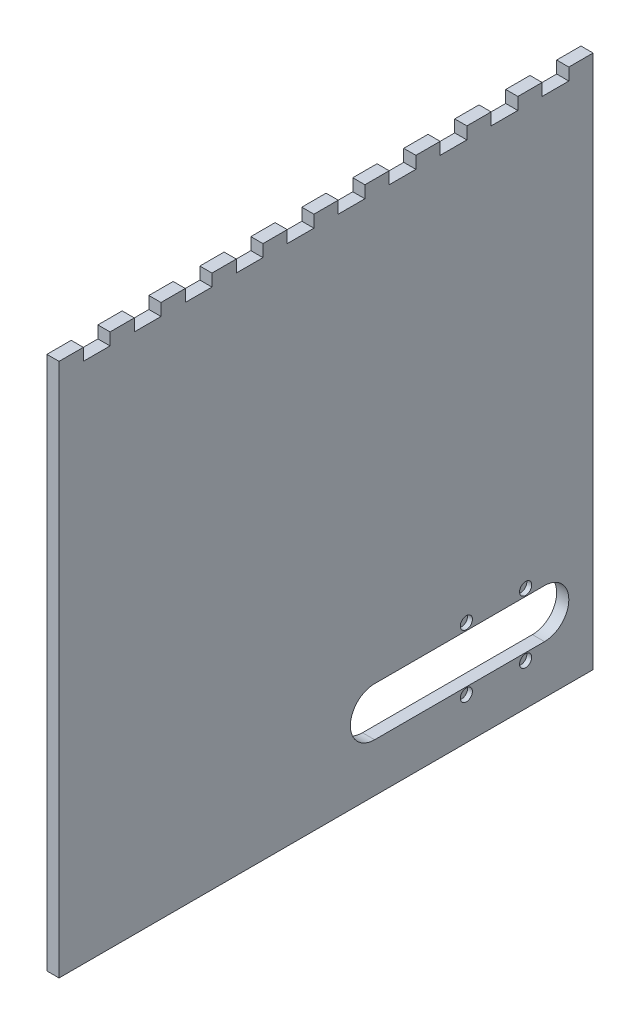
SolidWorks part; units mm, degrees
material "Acrylic (Medium-high impact)"
ref_plane "Front" through (0, 0, 0) normal (0, 0, 1) x (1, 0, 0)
ref_plane "Top" through (0, 0, 0) normal (0, 1, 0) x (1, 0, 0)
ref_plane "Right" through (0, 0, 0) normal (1, 0, 0) x (0, 0, -1)
sketch "Sketch1" plane through (0, 0, 0) normal (1, 0, 0) x (0, 0, -1)
  line L1 (-139.7, 142.875) -> (139.7, 142.875)
  line L2 (-139.7, 142.875) -> (-139.7, -142.875)
  line L3 (-139.7, -142.875) -> (139.7, -142.875)
  line L4 (139.7, 142.875) -> (139.7, -142.875)
  point P4 (-139.7, 0)
  point P6 (0, 142.875)
  dimension "D1" = 285.75
  dimension "D2" = 279.4
extrude "Boss-Extrude1" add sketch "Sketch1" along normal blind 6.35
sketch "Sketch2" plane through (6.35, 0, 0) normal (1, 0, 0) x (0, 0, -1)
  line L0 (139.7, -142.875) -> (139.7, 142.875) construction
  line L1 (-139.7, 142.875) -> (139.7, 142.875)
  line L2 (-139.7, 142.875) -> (-139.7, 136.525)
  line L3 (-139.7, 136.525) -> (139.7, 136.525)
  line L4 (139.7, 142.875) -> (139.7, 136.525)
  dimension "D1" = 6.35
extrude "Boss-Extrude2" add sketch "Sketch2" along normal blind 12.7
sketch "Sketch3" plane through (0, 0, 0) normal (-1, 0, 0) x (0, 0, 1)
  line L0 (-114.3, -85.725) -> (-25.4, -85.725)
  line L1 (-25.4, -111.125) -> (-114.3, -111.125)
  line L2 (12.7, 142.875) -> (12.7, -142.875) construction
  line L3 (-139.7, 142.875) -> (139.7, 142.875) construction
  line L4 (139.7, -142.875) -> (-139.7, -142.875) construction
  line L5 (139.7, 142.875) -> (139.7, -142.875) construction
  arc A0 (-25.4, -85.725) -> (-25.4, -111.125) centre (-25.4, -98.425) cw
  arc A1 (-114.3, -111.125) -> (-114.3, -85.725) centre (-114.3, -98.425) cw
  dimension "D1" = 25.4
  dimension "D3" = 88.9
  dimension "D2" = 38.1
  dimension "D4" = 127
  dimension "D5" = 44.45
extrude "Cut-Extrude1" cut sketch "Sketch3" against normal through all
sketch "Sketch4" plane through (0, 0, 0) normal (-1, 0, 0) x (0, 0, 1)
  line L0 (-113.03, 142.875) -> (-100.33, 142.875)
  line L1 (-139.7, 142.875) -> (-127, 142.875)
  line L2 (-139.7, 142.875) -> (-139.7, 136.525)
  line L3 (-139.7, 136.525) -> (-127, 136.525)
  line L4 (-127, 142.875) -> (-127, 136.525)
  line L5 (-113.03, 142.875) -> (-113.03, 136.525)
  line L6 (-113.03, 136.525) -> (-100.33, 136.525)
  line L7 (-100.33, 142.875) -> (-100.33, 136.525)
  line L8 (-86.36, 142.875) -> (-73.66, 142.875)
  line L9 (-86.36, 142.875) -> (-86.36, 136.525)
  line L10 (-86.36, 136.525) -> (-73.66, 136.525)
  line L11 (-73.66, 142.875) -> (-73.66, 136.525)
  line L12 (-59.69, 142.875) -> (-46.99, 142.875)
  line L13 (-59.69, 142.875) -> (-59.69, 136.525)
  line L14 (-59.69, 136.525) -> (-46.99, 136.525)
  line L15 (-46.99, 142.875) -> (-46.99, 136.525)
  line L16 (-33.02, 142.875) -> (-20.32, 142.875)
  line L17 (-33.02, 142.875) -> (-33.02, 136.525)
  line L18 (-33.02, 136.525) -> (-20.32, 136.525)
  line L19 (-20.32, 142.875) -> (-20.32, 136.525)
  line L20 (-6.35, 142.875) -> (6.35, 142.875)
  line L21 (-6.35, 142.875) -> (-6.35, 136.525)
  line L22 (-6.35, 136.525) -> (6.35, 136.525)
  line L23 (6.35, 142.875) -> (6.35, 136.525)
  line L24 (20.32, 142.875) -> (33.02, 142.875)
  line L25 (20.32, 142.875) -> (20.32, 136.525)
  line L26 (20.32, 136.525) -> (33.02, 136.525)
  line L27 (33.02, 142.875) -> (33.02, 136.525)
  line L28 (46.99, 142.875) -> (59.69, 142.875)
  line L29 (46.99, 142.875) -> (46.99, 136.525)
  line L30 (46.99, 136.525) -> (59.69, 136.525)
  line L31 (59.69, 142.875) -> (59.69, 136.525)
  line L32 (73.66, 142.875) -> (86.36, 142.875)
  line L33 (73.66, 142.875) -> (73.66, 136.525)
  line L34 (73.66, 136.525) -> (86.36, 136.525)
  line L35 (86.36, 142.875) -> (86.36, 136.525)
  line L36 (100.33, 142.875) -> (113.03, 142.875)
  line L37 (100.33, 142.875) -> (100.33, 136.525)
  line L38 (100.33, 136.525) -> (113.03, 136.525)
  line L39 (113.03, 142.875) -> (113.03, 136.525)
  line L40 (127, 142.875) -> (139.7, 142.875)
  line L41 (127, 142.875) -> (127, 136.525)
  line L42 (127, 136.525) -> (139.7, 136.525)
  line L43 (139.7, 142.875) -> (139.7, 136.525)
  line L69 (-139.7, 142.875) -> (139.7, 142.875)
  line L70 (-139.7, 142.875) -> (-139.7, 136.525)
  line L71 (-139.7, 136.525) -> (139.7, 136.525)
  line L72 (139.7, 142.875) -> (139.7, 136.525)
  line M74 (139.7, 142.875) -> (-139.7, 142.875)
  dimension "D1" = 6.35
  dimension "D2" = 12.7
  dimension "D3" = 11
sketch "Sketch5" plane through (0, 0, -139.7) normal (0, 0, -1) x (-1, 0, 0)
  line L1 (-6.35, 136.525) -> (-57.7651, 136.525)
  line L2 (-6.35, 136.525) -> (-6.35, 157.6842)
  line L3 (-6.35, 157.6842) -> (-57.7651, 157.6842)
  line L4 (-57.7651, 136.525) -> (-57.7651, 157.6842)
extrude "Cut-Extrude2" cut sketch "Sketch5" against normal through all
extrude "Cut-Extrude3" cut sketch "Sketch4" against normal blind 6.35 contours L4 L71 L5 M74 | L7 L71 L9 M74 | L11 L71 L13 M74 | L15 L71 L17 M74 | L19 L71 L21 M74 | L23 L71 L25 M74 | L27 L71 L29 M74 | L31 L71 L33 M74 | L35 L71 L37 M74 | L39 L71 L41 M74 | L69
sketch "Sketch6" plane through (6.35, 0, 0) normal (1, 0, 0) x (0, 0, -1)
  line L0 (77.9, -100.965) -> (77.9, -95.885)
  line L1 (99.9, -95.885) -> (99.9, -100.965)
  line L2 (71.9, -116.465) -> (71.9, -111.385)
  line L3 (74.9, -116.465) -> (74.9, -111.385)
  line L4 (71.9, -85.465) -> (71.9, -80.385)
  line L5 (74.9, -85.465) -> (74.9, -80.385)
  line L6 (88.9, -95.885) -> (88.9, -100.965) construction
  line L7 (105.9, -116.465) -> (105.9, -111.385)
  line L8 (102.9, -116.465) -> (102.9, -111.385)
  line L9 (102.9, -85.465) -> (102.9, -80.385)
  line L10 (105.9, -85.465) -> (105.9, -80.385)
  line L11 (-139.7, 142.875) -> (-139.7, -142.875) construction
  line L12 (-139.7, -142.875) -> (139.7, -142.875) construction
  arc A0 (77.9, -100.965) -> (99.9, -100.965) centre (88.9, -100.965) ccw
  arc A1 (99.9, -95.885) -> (77.9, -95.885) centre (88.9, -95.885) ccw
  arc A2 (71.9, -116.465) -> (74.9, -116.465) centre (73.4, -116.465) ccw
  arc A3 (74.9, -111.385) -> (71.9, -111.385) centre (73.4, -111.385) ccw
  arc A4 (71.9, -85.465) -> (74.9, -85.465) centre (73.4, -85.465) ccw
  arc A5 (74.9, -80.385) -> (71.9, -80.385) centre (73.4, -80.385) ccw
  arc A6 (105.9, -116.465) -> (102.9, -116.465) centre (104.4, -116.465) cw
  arc A7 (102.9, -111.385) -> (105.9, -111.385) centre (104.4, -111.385) cw
  arc A8 (105.9, -85.465) -> (102.9, -85.465) centre (104.4, -85.465) cw
  arc A9 (102.9, -80.385) -> (105.9, -80.385) centre (104.4, -80.385) cw
  circle A10 centre (73.4, -82.06) radius 3.175
  circle A11 centre (104.4, -82.06) radius 3.175
  circle A12 centre (73.4, -114.79) radius 3.175
  circle A13 centre (104.4, -114.79) radius 3.175
  point P37 (88.9, -98.425)
  point P38 (99.9, -98.425)
  dimension "D5" = 1.5
  dimension "D9" = 1.5
  dimension "D12" = 6.35
  dimension "D1" = 5.08
  dimension "D2" = 5.08
  dimension "D3" = 15.5
  dimension "D4" = 15.5
  dimension "D6" = 15.5
  dimension "D7" = 15.5
  dimension "D8" = 5.08
  dimension "D10" = 228.6
  dimension "D11" = 44.45
extrude "Cut-Extrude5" cut sketch "Sketch6" against normal blind 2.54 contours L5 A10 A5 | L4 A10 L5 A5 | A5 A10 L4 | L9 A11 L10 A9 | A9 A11 L9 | L10 A11 A9 | A2 A12 L3 | L3 A12 L2 A2 | L2 A12 A2 | L7 A13 L8 A6 | A6 A13 L7 | L8 A13 A6
sketch "Sketch7" plane through (6.35, 0, 0) normal (1, 0, 0) x (0, 0, -1)
  line L0 (-139.7, 142.875) -> (-139.7, -142.875) construction
  line L1 (-139.7, -136.525) -> (139.7, -136.525)
  line L2 (-139.7, -136.525) -> (-139.7, -142.875)
  line L3 (-139.7, -142.875) -> (139.7, -142.875)
  line L4 (139.7, -136.525) -> (139.7, -142.875)
  line L5 (-139.7, -142.875) -> (139.7, -142.875) construction
  line L6 (139.7, -142.875) -> (139.7, 142.875) construction
  point P8 (139.7, -130.175)
  dimension "D1" = 6.35
extrude "Cut-Extrude6" cut sketch "Sketch7" against normal through all
